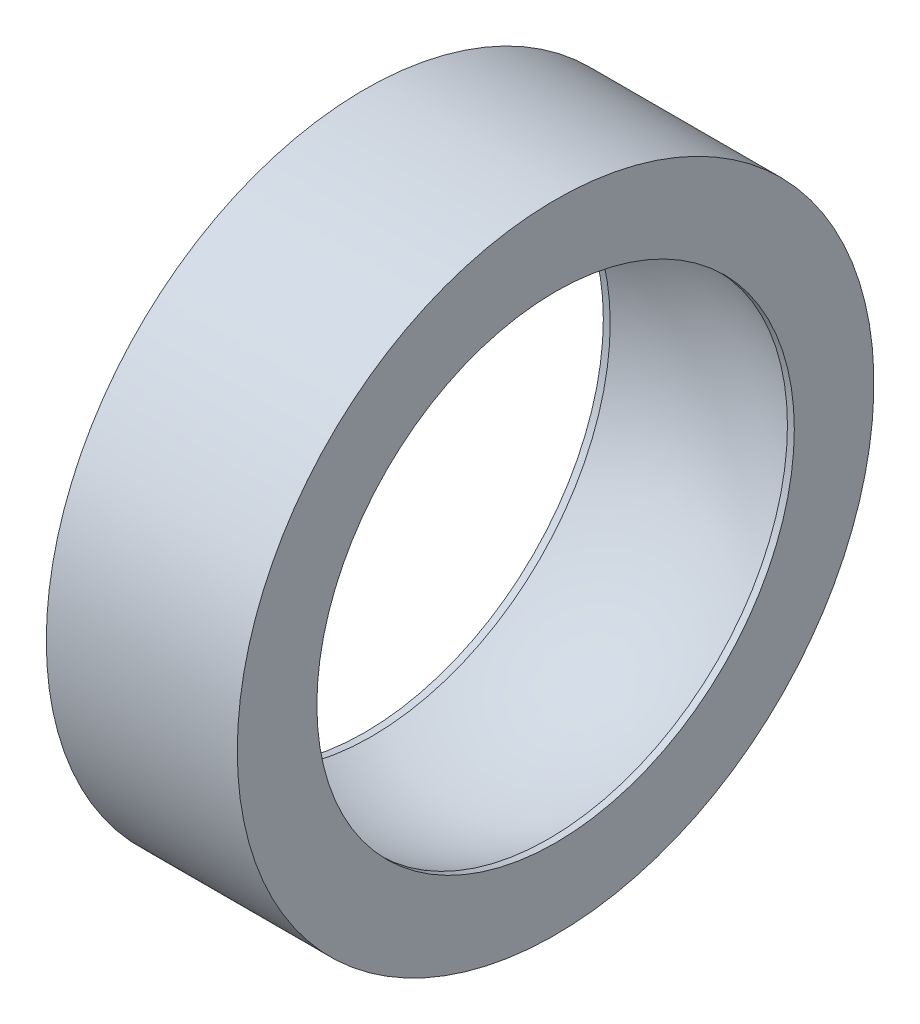
SolidWorks part; units mm, degrees
ref_plane "Front Plane" through (0, 0, 0) normal (0, 0, 1) x (1, 0, 0)
ref_plane "Top Plane" through (0, 0, 0) normal (0, 1, 0) x (1, 0, 0)
ref_plane "Right Plane" through (0, 0, 0) normal (1, 0, 0) x (0, 0, -1)
sketch "Sketch1" plane through (0, 0, 0) normal (0, 0, 1) x (1, 0, 0)
  line L0 (-10.16, 0) -> (12.9754, 0) construction
  line L2 (3.048, 10.16) -> (-3.048, 10.16)
  line L3 (3.048, 10.16) -> (3.048, 7.62)
  line L5 (-3.048, 10.16) -> (-3.048, 7.62)
  line L6 (3.048, 10.16) -> (-3.048, 7.62) construction
  line L7 (3.048, 7.62) -> (-3.048, 10.16) construction
  line L8 (-3.048, 7.62) -> (-2.8284, 7.62)
  line L9 (2.8284, 7.62) -> (3.048, 7.62)
  arc A0 (-2.8284, 7.62) -> (2.8284, 7.62) centre (0, 0) cw
  point P3 (0, 8.89)
  point P8 (0, 10.16)
  dimension "D4" = 8.128
  dimension "D1" = 6.096
  dimension "D2" = 10.16
  dimension "D3" = 2.54
revolve "Revolve1" add sketch "Sketch1" angle 360 about L0
